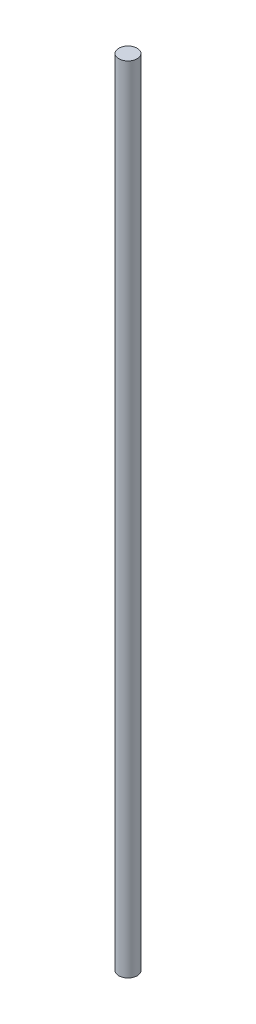
SolidWorks part; units mm, degrees
ref_plane "Front Plane" through (0, 0, 0) normal (0, 0, 1) x (1, 0, 0)
ref_plane "Top Plane" through (0, 0, 0) normal (0, 1, 0) x (1, 0, 0)
ref_plane "Right Plane" through (0, 0, 0) normal (1, 0, 0) x (0, 0, -1)
sketch "Sketch1" plane through (0, 0, 0) normal (0, 1, 0) x (1, 0, 0)
  circle A0 centre (0, 0) radius 7.5
extrude "Boss-Extrude1" add sketch "Sketch1" against normal blind 650
